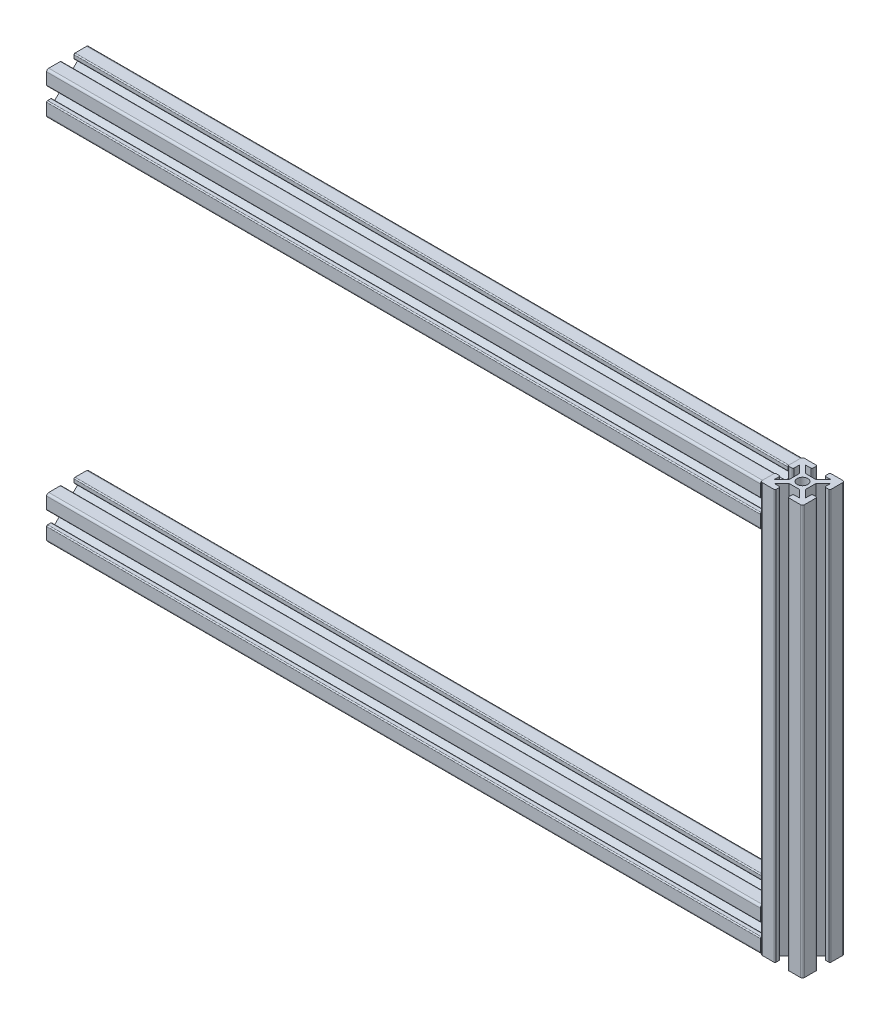
SolidWorks part; units mm, degrees
ref_plane "Front Plane" through (0, 0, 0) normal (0, 0, 1) x (1, 0, 0)
ref_plane "Top Plane" through (0, 0, 0) normal (0, 1, 0) x (1, 0, 0)
ref_plane "Right Plane" through (0, 0, 0) normal (1, 0, 0) x (0, 0, -1)
sketch "Sketch2" plane through (0, 0, 0) normal (0, 0, 1) x (1, 0, 0)
  line L0 (0, 0) -> (350, 0)
  line L1 (350, 0) -> (350, -175)
  line L2 (350, -175) -> (0, -175)
  dimension "D1" = 350
  dimension "D2" = 350
  dimension "D3" = 175
other "Aluminium prof ALUMINIUM PROF(1)"
ref_plane "Plane2" through (0, 0, 0) normal (1, 0, 0) x (0, 1, 0)
sketch "Sketch1" plane through (0, 0, 0) normal (1, 0, 0) x (0, 1, 0)
  line L0 (0, 0) -> (0, 19.0058) construction
  line L9 (0, 0) -> (23.0409, 0) construction
  line L10 (23.0409, 0) -> (23.0409, -0.0585) construction
  line L11 (23.0409, -0.0585) -> (23.0409, 0) construction
  line L13 (-2.5, 4) -> (2.5, 4)
  line L14 (2.5, 4) -> (6.0355, 7.5355)
  line L15 (6.0355, 7.5355) -> (3.5355, 7.5355)
  line L16 (3.0355, 8.0355) -> (3.0355, 9.5355)
  line L17 (3.5355, 10.0355) -> (9.0355, 10.0355)
  line L18 (10.0355, 9.0355) -> (10.0355, 3.5355)
  line L19 (9.5355, 3.0355) -> (8.0355, 3.0355)
  line L20 (7.5355, 3.5355) -> (7.5355, 6.0355)
  line L21 (7.5355, 6.0355) -> (4, 2.5)
  line L22 (4, 2.5) -> (4, -2.5)
  line L23 (-10.0355, 9.0355) -> (-10.0355, 3.5355)
  line L24 (-4, 2.5) -> (-4, -2.5)
  line L25 (-7.5355, 6.0355) -> (-4, 2.5)
  line L26 (-7.5355, 3.5355) -> (-7.5355, 6.0355)
  line L27 (-9.5355, 3.0355) -> (-8.0355, 3.0355)
  line L28 (-3.5355, 10.0355) -> (-9.0355, 10.0355)
  line L29 (-3.0355, 8.0355) -> (-3.0355, 9.5355)
  line L30 (-6.0355, 7.5355) -> (-3.5355, 7.5355)
  line L31 (-2.5, 4) -> (-6.0355, 7.5355)
  line L32 (3.5355, -10.0355) -> (9.0355, -10.0355)
  line L33 (-2.5, -4) -> (-6.0355, -7.5355)
  line L34 (-6.0355, -7.5355) -> (-3.5355, -7.5355)
  line L35 (-3.0355, -8.0355) -> (-3.0355, -9.5355)
  line L36 (-3.5355, -10.0355) -> (-9.0355, -10.0355)
  line L37 (-9.5355, -3.0355) -> (-8.0355, -3.0355)
  line L38 (-7.5355, -3.5355) -> (-7.5355, -6.0355)
  line L39 (-7.5355, -6.0355) -> (-4, -2.5)
  line L40 (-10.0355, -9.0355) -> (-10.0355, -3.5355)
  line L41 (7.5355, -6.0355) -> (4, -2.5)
  line L42 (7.5355, -3.5355) -> (7.5355, -6.0355)
  line L43 (9.5355, -3.0355) -> (8.0355, -3.0355)
  line L44 (10.0355, -9.0355) -> (10.0355, -3.5355)
  line L45 (3.0355, -8.0355) -> (3.0355, -9.5355)
  line L46 (6.0355, -7.5355) -> (3.5355, -7.5355)
  line L47 (2.5, -4) -> (6.0355, -7.5355)
  line L48 (-2.5, -4) -> (2.5, -4)
  circle A0 centre (0, 0) radius 2.5
  arc A1 (-10.0355, 9.0355) -> (-9.0355, 10.0355) centre (-9.0355, 9.0355) cw
  arc A2 (-9.0355, -10.0355) -> (-10.0355, -9.0355) centre (-9.0355, -9.0355) cw
  arc A3 (9.0355, -10.0355) -> (10.0355, -9.0355) centre (9.0355, -9.0355) ccw
  arc A4 (9.0355, 10.0355) -> (10.0355, 9.0355) centre (9.0355, 9.0355) cw
  arc A5 (-9.5355, -3.0355) -> (-10.0355, -3.5355) centre (-9.5355, -3.5355) ccw
  arc A6 (-8.0355, -3.0355) -> (-7.5355, -3.5355) centre (-8.0355, -3.5355) cw
  arc A7 (-3.5355, -7.5355) -> (-3.0355, -8.0355) centre (-3.5355, -8.0355) cw
  arc A8 (-3.0355, -9.5355) -> (-3.5355, -10.0355) centre (-3.5355, -9.5355) cw
  arc A9 (3.5355, -10.0355) -> (3.0355, -9.5355) centre (3.5355, -9.5355) cw
  arc A10 (3.0355, -8.0355) -> (3.5355, -7.5355) centre (3.5355, -8.0355) cw
  arc A11 (9.5355, -3.0355) -> (10.0355, -3.5355) centre (9.5355, -3.5355) cw
  arc A12 (7.5355, -3.5355) -> (8.0355, -3.0355) centre (8.0355, -3.5355) cw
  arc A13 (10.0355, 3.5355) -> (9.5355, 3.0355) centre (9.5355, 3.5355) cw
  arc A14 (8.0355, 3.0355) -> (7.5355, 3.5355) centre (8.0355, 3.5355) cw
  arc A15 (3.5355, 7.5355) -> (3.0355, 8.0355) centre (3.5355, 8.0355) cw
  arc A16 (3.0355, 9.5355) -> (3.5355, 10.0355) centre (3.5355, 9.5355) cw
  arc A17 (-3.5355, 10.0355) -> (-3.0355, 9.5355) centre (-3.5355, 9.5355) cw
  arc A18 (-3.0355, 8.0355) -> (-3.5355, 7.5355) centre (-3.5355, 8.0355) cw
  arc A19 (-7.5355, 3.5355) -> (-8.0355, 3.0355) centre (-8.0355, 3.5355) cw
  arc A20 (-10.0355, 3.5355) -> (-9.5355, 3.0355) centre (-9.5355, 3.5355) ccw
  point P26 (0, 4)
  point P29 (-4, 0)
  point P30 (4, 0)
  point P44 (0, -4)
  point P48 (-10.0355, 10.0355)
  point P51 (-10.0355, -10.0355)
  point P54 (10.0355, -10.0355)
  point P57 (10.0355, 10.0355)
  point P60 (-10.0355, -3.0355)
  point P63 (-7.5355, -3.0355)
  point P66 (-3.0355, -7.5355)
  point P69 (-3.0355, -10.0355)
  point P72 (3.0355, -10.0355)
  point P75 (3.0355, -7.5355)
  point P78 (10.0355, -3.0355)
  point P81 (7.5355, -3.0355)
  point P84 (10.0355, 3.0355)
  point P87 (7.5355, 3.0355)
  point P90 (3.0355, 7.5355)
  point P93 (3.0355, 10.0355)
  point P96 (-3.0355, 10.0355)
  point P99 (-3.0355, 7.5355)
  point P102 (-7.5355, 3.0355)
  point P105 (-10.0355, 3.0355)
  point P106 (0, 0)
  dimension "D5" = 4
  dimension "D12" = 1
  dimension "D13" = 0.5
  dimension "D1" = 135
  dimension "D2" = 2.5
  dimension "D3" = 4
  dimension "D4" = 2.5
  dimension "D6" = 7
  dimension "D7" = 7
  dimension "D8" = 3
  dimension "D9" = 3
  dimension "D10" = 5
  dimension "D11" = 23.0409
other "Trim/Extend1"
other "Trim/Extend2"
sketch "Sketch3" plane through (0, 4, 0) normal (0, 1, 0) x (1, 0, 0)
  line L0 (0, 0) -> (408.1297, 0) construction
  line L2 (0, 2.5) -> (0, -2.5) construction
  circle A0 centre (75, 0) radius 2.5
  circle A1 centre (175, 0) radius 2.5
  circle A2 centre (264.9645, 0) radius 2.5
  dimension "D1" = 5
  dimension "D2" = 75
  dimension "D3" = 75
  dimension "D4" = 100
  dimension "D5" = 89.9645
extrude "Cut-Extrude1" cut sketch "Sketch3" against normal blind 10
